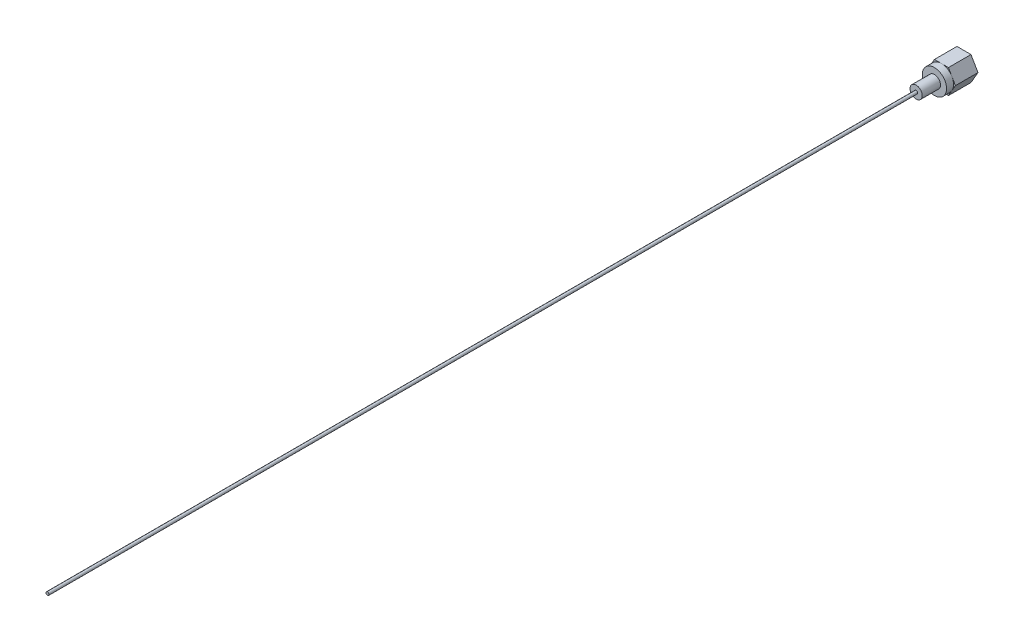
SolidWorks part; units mm, degrees
ref_plane "Alzado" through (0, 0, 0) normal (0, 0, 1) x (1, 0, 0)
ref_plane "Planta" through (0, 0, 0) normal (0, 1, 0) x (1, 0, 0)
ref_plane "Vista lateral" through (0, 0, 0) normal (1, 0, 0) x (0, 0, -1)
sketch "Sketch1" plane through (0, 0, 0) normal (0, 0, 1) x (1, 0, 0)
  line L1 (2.3, -3.9837) -> (4.6, 0)
  line L2 (4.6, 0) -> (2.3, 3.9837)
  line L3 (2.3, 3.9837) -> (-2.3, 3.9837)
  line L4 (-2.3, 3.9837) -> (-4.6, 0)
  line L5 (-4.6, 0) -> (-2.3, -3.9837)
  line L6 (-2.3, -3.9837) -> (2.3, -3.9837)
  circle A0 centre (0, 0) radius 3.9837 construction
  point P1 (-4.6, 0)
  point P10 (0, 0)
  point P11 (0, 0)
  dimension "D1" = 4.6
extrude "Boss-Extrude1" add sketch "Sketch1" along normal blind 7.4
sketch "Sketch2" plane through (0, 0, 7.4) normal (0, 0, 1) x (1, 0, 0)
  line L0 (-2.3, 3.9837) -> (-4.6, 0) construction
  circle A0 centre (0, 0) radius 3.9837
extrude "Boss-Extrude2" add sketch "Sketch2" along normal blind 2.3
sketch "Sketch3" plane through (0, 0, 9.7) normal (0, 0, 1) x (1, 0, 0)
  circle A0 centre (0, 0) radius 2
  dimension "D1" = 4
extrude "Boss-Extrude3" add sketch "Sketch3" along normal blind 6
sketch "Sketch4" plane through (0, 0, 15.7) normal (0, 0, 1) x (1, 0, 0)
  circle A0 centre (0, 0) radius 0.5
  point P3 (0, 0)
  dimension "D1" = 1
extrude "Boss-Extrude4" add sketch "Sketch4" along normal blind 285
